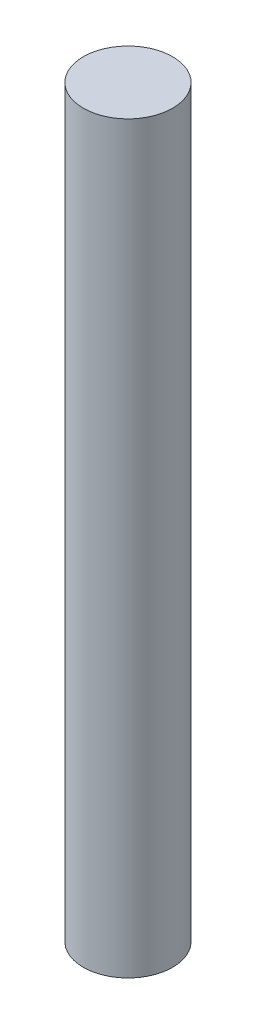
SolidWorks part; units mm, degrees
ref_plane "Front Plane" through (0, 0, 0) normal (0, 0, 1) x (1, 0, 0)
ref_plane "Top Plane" through (0, 0, 0) normal (0, 1, 0) x (1, 0, 0)
ref_plane "Right Plane" through (0, 0, 0) normal (1, 0, 0) x (0, 0, -1)
sketch "Sketch1" plane through (0, 0, 0) normal (0, 1, 0) x (1, 0, 0)
  circle A0 centre (0, 0) radius 3
  dimension "D1" = 6
extrude "Boss-Extrude1" add sketch "Sketch1" along normal blind 50
